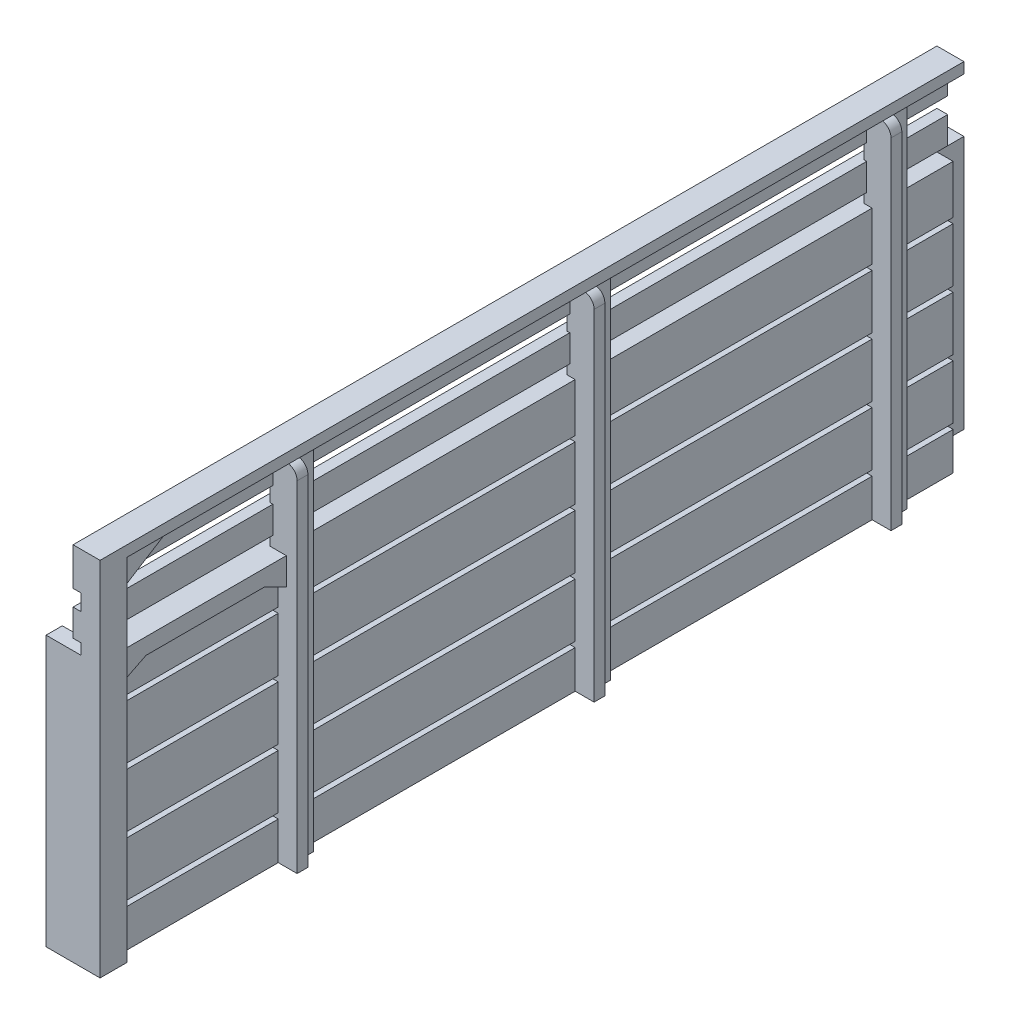
SolidWorks part; units mm, degrees
ref_plane "Front Plane" through (0, 0, 0) normal (0, 0, 1) x (1, 0, 0)
ref_plane "Top Plane" through (0, 0, 0) normal (0, 1, 0) x (1, 0, 0)
ref_plane "Right Plane" through (0, 0, 0) normal (1, 0, 0) x (0, 0, -1)
sketch "Sketch1" plane through (0, 0, 0) normal (1, 0, 0) x (0, 0, -1)
  line L1 (-80, 25) -> (80, 25)
  line L2 (-80, 25) -> (-80, -25)
  line L3 (-80, -25) -> (80, -25)
  line L4 (80, 25) -> (80, -25)
  line L5 (-80, 25) -> (80, -25) construction
  line L6 (-80, -25) -> (80, 25) construction
  point P0 (0, 0)
  dimension "D1" = 160
  dimension "D2" = 50
extrude "Boss-Extrude1" add sketch "Sketch1" along normal blind 3
sketch "Sketch2" plane through (3, 0, 0) normal (1, 0, 0) x (0, 0, -1)
  line L0 (80, -25) -> (80, 25) construction
  line L1 (80, -18) -> (-80, -18)
  line L2 (80, -18) -> (80, -17)
  line L3 (80, -17) -> (-80, -17)
  line L4 (-80, -18) -> (-80, -17)
  line L5 (-80, 25) -> (-80, -25) construction
  line L6 (-80, -25) -> (80, -25) construction
  line L8 (80, -7) -> (-80, -7)
  line L9 (80, -7) -> (80, -6)
  line L10 (80, -6) -> (-80, -6)
  line L11 (-80, -7) -> (-80, -6)
  line L12 (-80, 5) -> (80, 5)
  line L13 (-80, 5) -> (-80, 4)
  line L14 (-80, 4) -> (80, 4)
  line L15 (80, 5) -> (80, 4)
  line L16 (-80, 16) -> (80, 16)
  line L17 (-80, 16) -> (-80, 15)
  line L18 (-80, 15) -> (80, 15)
  line L19 (80, 16) -> (80, 15)
  dimension "D1" = 1
  dimension "D2" = 7
  dimension "D3" = 10
  dimension "D4" = 1
  dimension "D5" = 10
  dimension "D6" = 1
  dimension "D7" = 1
  dimension "D8" = 10
extrude "Cut-Extrude1" cut sketch "Sketch2" against normal blind 1.5
sketch "Sketch3" plane through (3, 0, 0) normal (1, 0, 0) x (0, 0, -1)
  line L0 (-80, -25) -> (80, -25) construction
  line L1 (-80, -25) -> (-75, -25)
  line L2 (-80, -25) -> (-80, 40)
  line L3 (-80, 40) -> (-75, 40)
  line L4 (-75, -25) -> (-75, 40)
  line L5 (-45, -25) -> (-40, -25)
  line L6 (-45, -25) -> (-45, 40)
  line L7 (-45, 40) -> (-40, 40)
  line L8 (-40, -25) -> (-40, 40)
  line L10 (10, -25) -> (15, -25)
  line L11 (10, -25) -> (10, 40)
  line L12 (10, 40) -> (15, 40)
  line L13 (15, -25) -> (15, 40)
  line L14 (65, -25) -> (70, -25)
  line L15 (65, -25) -> (65, 40)
  line L16 (65, 40) -> (70, 40)
  line L17 (70, -25) -> (70, 40)
  dimension "D1" = 5
  dimension "D2" = 65
  dimension "D3" = 5
  dimension "D4" = 65
  dimension "D5" = 30
  dimension "D6" = 5
  dimension "D7" = 65
  dimension "D8" = 50
  dimension "D9" = 5
  dimension "D10" = 50
  dimension "D11" = 65
extrude "Boss-Extrude2" add sketch "Sketch3" along normal mid plane 3
sketch "Sketch4" plane through (0, 0, 0) normal (-1, 0, 0) x (0, 0, 1)
  line L0 (80, 25) -> (80, -25) construction
  line L1 (-80, -25) -> (80, -25)
  line L2 (-80, -25) -> (-80, -22)
  line L3 (-80, -22) -> (80, -22)
  line L4 (80, -25) -> (80, -22)
  dimension "D1" = 3
extrude "Boss-Extrude3" add sketch "Sketch4" along normal blind 5
sketch "Sketch5" plane through (0, 0, 0) normal (-1, 0, 0) x (0, 0, 1)
  line L0 (80, -22) -> (-80, -22) construction
  line L1 (80, 25) -> (77, 25)
  line L2 (80, 25) -> (80, -22)
  line L3 (80, -22) -> (77, -22)
  line L4 (77, 25) -> (77, -22)
  dimension "D1" = 3
extrude "Boss-Extrude4" add sketch "Sketch5" along normal blind 5
sketch "Sketch6" plane through (0, 0, 0) normal (-1, 0, 0) x (0, 0, 1)
  line L0 (80, 40) -> (80, 25) construction
  line L1 (80, 27) -> (-80, 27)
  line L2 (80, 27) -> (80, 32)
  line L3 (80, 32) -> (-80, 32)
  line L4 (-80, 27) -> (-80, 32)
  line L5 (-80, 25) -> (77, 25) construction
  line L7 (80, 35) -> (-80, 35)
  line L8 (80, 35) -> (80, 40)
  line L9 (80, 40) -> (-80, 40)
  line L10 (-80, 35) -> (-80, 40)
  dimension "D1" = 160
  dimension "D2" = 5
  dimension "D3" = 2
  dimension "D4" = 160
  dimension "D5" = 5
  dimension "D6" = 3
extrude "Boss-Extrude5" add sketch "Sketch6" against normal blind 2
sketch "Sketch7" plane through (4.5, 0, 0) normal (1, 0, 0) x (0, 0, -1)
  line L0 (-45, 40) -> (-45, -25) construction
  line L1 (-45, -25) -> (-43, -25)
  line L2 (-45, -25) -> (-45, 40)
  line L3 (-45, 40) -> (-43, 40)
  line L4 (-43, -25) -> (-43, 40)
  line L5 (-45, -25) -> (-40, -25) construction
  line L6 (-40, 40) -> (-45, 40) construction
  line L7 (15, 40) -> (10, 40) construction
  line L8 (10, -25) -> (12, -25)
  line L9 (10, -25) -> (10, 40)
  line L10 (10, 40) -> (12, 40)
  line L11 (12, -25) -> (12, 40)
  line L12 (70, 40) -> (65, 40) construction
  line L13 (65, -25) -> (67, -25)
  line L14 (65, -25) -> (65, 40)
  line L15 (65, 40) -> (67, 40)
  line L16 (67, -25) -> (67, 40)
  dimension "D1" = 65
  dimension "D2" = 2
  dimension "D3" = 2
  dimension "D4" = 65
  dimension "D5" = 2
  dimension "D6" = 65
extrude "Boss-Extrude6" add sketch "Sketch7" along normal blind 2
fillet "Fillet1" radius 2 3 edges at (6.5, 40, -66) (6.5, 40, -11) (6.5, 40, 44)
sketch "Sketch8" plane through (0, 40, 0) normal (0, 1, 0) x (1, 0, 0)
  line L1 (2, 80) -> (0, 80) construction
  line L2 (0, -80) -> (5, -80)
  line L3 (0, -80) -> (0, 80)
  line L4 (0, 80) -> (5, 80)
  line L5 (5, -80) -> (5, 80)
  dimension "D1" = 5
extrude "Boss-Extrude7" add sketch "Sketch8" along normal blind 2
sketch "Sketch9" plane through (0, 0, 0) normal (-1, 0, 0) x (0, 0, 1)
  line L0 (77, -22) -> (-80, -22) construction
  line L1 (-85, 25) -> (-75, 25)
  line L2 (-85, 25) -> (-85, -22)
  line L3 (-85, -22) -> (-75, -22)
  line L4 (-75, 25) -> (-75, -22)
  line L5 (-80, -22) -> (-80, 25) construction
  dimension "D1" = 10
  dimension "D2" = 5
  dimension "D3" = 47
extrude "Boss-Extrude8" add sketch "Sketch9" along normal up to surface (5 mm away) up to face at (-5, -7.3333, 25.6667)
sketch "Sketch10" plane through (2, 0, 0) normal (1, 0, 0) x (0, 0, -1)
  line L0 (-75, 40) -> (-75, 35) construction
  line L1 (-75, 40) -> (-75, 35)
  line L2 (-75, 40) -> (-45, 40) construction
  line L3 (-75, 40) -> (-67, 40)
  line L4 (-75, 35) -> (-67, 40)
  dimension "D1" = 8
extrude "Boss-Extrude9" add sketch "Sketch10" along normal up to surface (2.5 mm away) up to face at (4.5, 7.5, 77.5)
sketch "Sketch11" plane through (3, 0, 0) normal (1, 0, 0) x (0, 0, -1)
  line L0 (-45, 25) -> (-75, 25) construction
  line L1 (-45, 25) -> (-75, 25)
  line L2 (-75, 25) -> (-75, 16) construction
  line L3 (-75, 25) -> (-75, 20)
  line L4 (-45, 16) -> (-45, 25) construction
  line L5 (-45, 20) -> (-45, 25)
  line L6 (-75, 20) -> (-71, 22)
  line L7 (-71, 22) -> (-49, 22)
  line L8 (-49, 22) -> (-45, 20)
  dimension "D1" = 3
  dimension "D2" = 4
  dimension "D3" = 4
  dimension "D4" = 5
  dimension "D5" = 5
extrude "Boss-Extrude10" add sketch "Sketch11" along normal up to surface (1.5 mm away) up to face at (4.5, 13, 75.4)
sketch "Sketch12" plane through (4.5, 0, 0) normal (1, 0, 0) x (0, 0, -1)
  line L0 (-80, 40) -> (80, 40) construction
  line L1 (-80, -25) -> (-75.0329, -25)
  line L2 (-80, -25) -> (-80, 40)
  line L3 (-80, 40) -> (-75.0329, 40)
  line L4 (-75.0329, -25) -> (-75.0329, 40)
extrude "Boss-Extrude11" add sketch "Sketch12" along normal up to surface (0.5 mm away) up to face at (5, 41, 0)
